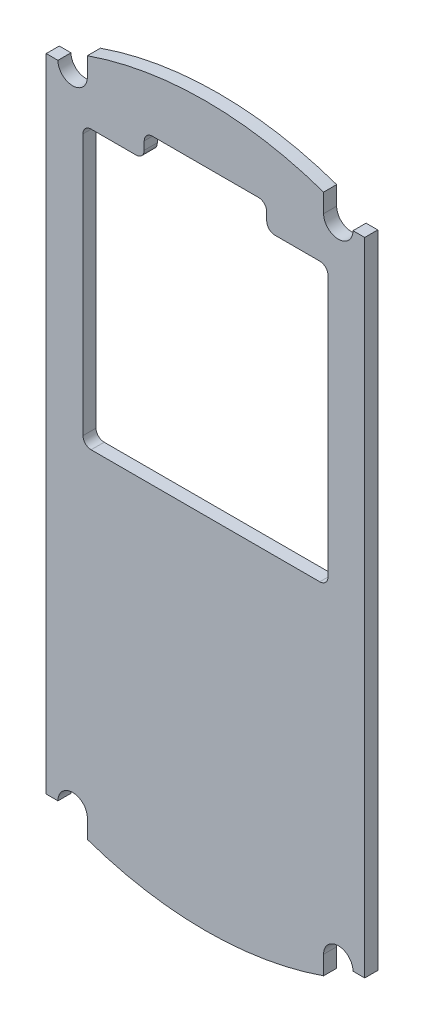
SolidWorks part; units mm, degrees
ref_plane "前视基准面" through (0, 0, 0) normal (0, 0, 1) x (1, 0, 0)
ref_plane "上视基准面" through (0, 0, 0) normal (0, 1, 0) x (1, 0, 0)
ref_plane "右视基准面" through (0, 0, 0) normal (1, 0, 0) x (0, 0, -1)
sketch "草图1" plane through (0, 0, 0) normal (0, 0, 1) x (1, 0, 0)
  line L2 (-19.5, 0) -> (-19.5, 39.2649)
  line L3 (19.5, 0) -> (19.5, 39.2649)
  line L4 (18.064, -39.2649) -> (19.5, -39.2649)
  line L5 (-18.064, 39.2649) -> (-19.5, 39.2649)
  line L6 (-14.464, 41.5547) -> (-14.464, 39.2649)
  line L7 (14.464, 41.5547) -> (14.464, 39.2649)
  line L8 (18.064, 39.2649) -> (19.5, 39.2649)
  line L9 (14.464, -41.5547) -> (14.464, -39.2649)
  line L10 (-14.464, -41.5547) -> (-14.464, -39.2649)
  line L11 (-18.064, -39.2649) -> (-19.5, -39.2649)
  line L12 (-19.5, 0) -> (-19.5, -39.2649)
  line L13 (19.5, 0) -> (19.5, -39.2649)
  arc A0 (14.464, 41.5547) -> (-14.464, 41.5547) centre (0, 0) ccw
  arc A2 (18.064, 39.2649) -> (14.464, 39.2649) centre (16.264, 39.2649) cw
  arc A3 (-18.064, 39.2649) -> (-14.464, 39.2649) centre (-16.264, 39.2649) ccw
  arc A4 (-18.064, -39.2649) -> (-14.464, -39.2649) centre (-16.264, -39.2649) cw
  arc A5 (18.064, -39.2649) -> (14.464, -39.2649) centre (16.264, -39.2649) ccw
  arc A6 (14.464, -41.5547) -> (-14.464, -41.5547) centre (0, 0) cw
extrude "凸台-拉伸1" add sketch "草图1" along normal blind 1.6
sketch "草图2" plane through (0, 0, 1.6) normal (0, 0, 1) x (1, 0, 0)
  line L1 (-15, 0) -> (15, 0)
  line L2 (15, 0) -> (15, 34)
  line L3 (7.5, 37) -> (-7.5, 37)
  line L4 (-15, 0) -> (-15, 34)
  line L5 (7.5, 34) -> (15, 34)
  line L6 (-7.5, 34) -> (-7.5, 37)
  line L7 (-7.5, 34) -> (-15, 34)
  line L8 (7.5, 34) -> (7.5, 37)
  point P0 (0, 0)
  point P7 (0, 36.5)
extrude "切除-拉伸1" cut sketch "草图2" against normal blind 10
fillet "圆角2" radius 1 8 edges at (15, 0, 0.8) (15, 34, 0.8) (7.5, 34, 0.8) (7.5, 37, 0.8) (-7.5, 37, 0.8) (-7.5, 34, 0.8) (-15, 0, 0.8) (-15, 34, 0.8)
